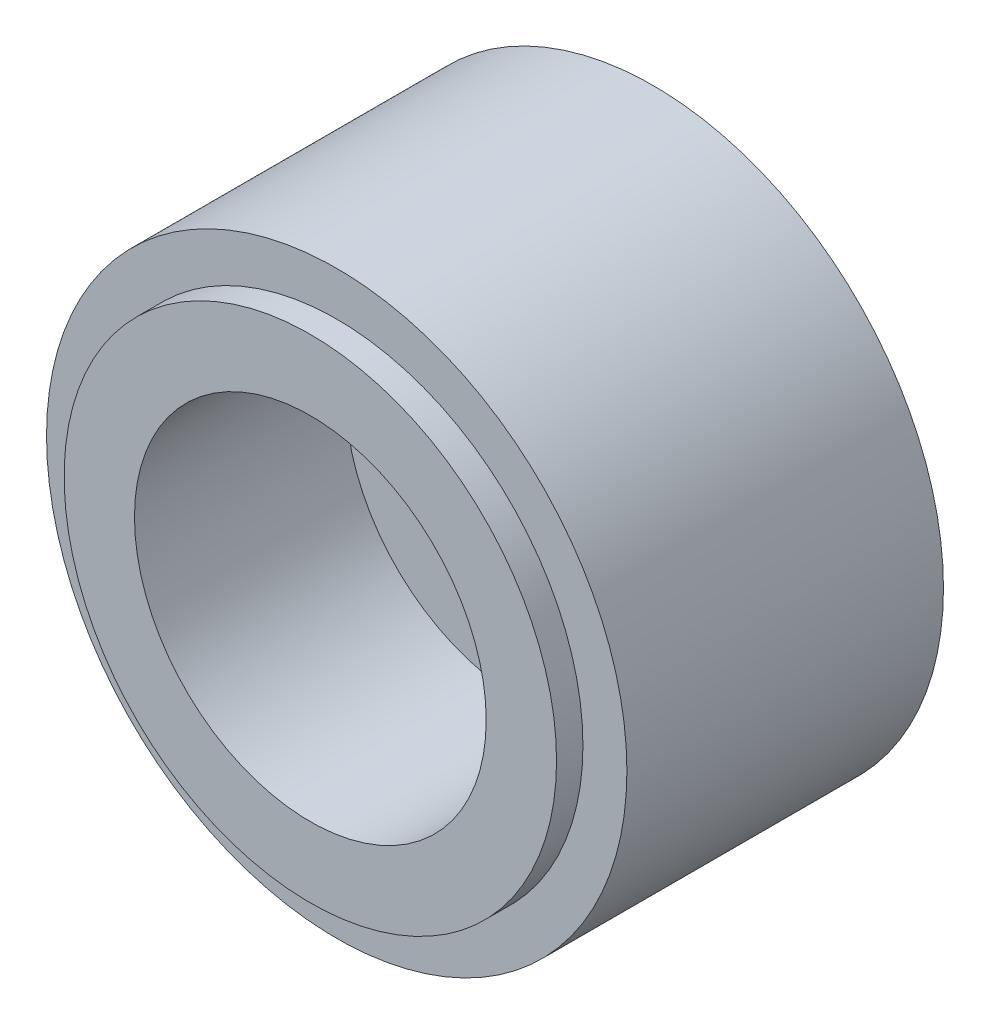
SolidWorks part; units mm, degrees
ref_plane "Front Plane" through (0, 0, 0) normal (0, 0, 1) x (1, 0, 0)
ref_plane "Top Plane" through (0, 0, 0) normal (0, 1, 0) x (1, 0, 0)
ref_plane "Right Plane" through (0, 0, 0) normal (1, 0, 0) x (0, 0, -1)
sketch "Sketch1" plane through (0, 0, 0) normal (0, 0, 1) x (1, 0, 0)
  circle A0 centre (0, 0) radius 14
  circle A1 centre (0, 0) radius 1.5
  dimension "D1" = 28
  dimension "D2" = 3
extrude "Boss-Extrude1" add sketch "Sketch1" along normal blind 1.5
sketch "Sketch2" plane through (0, 0, 1.5) normal (0, 0, 1) x (1, 0, 0)
  circle A0 centre (0, 0) radius 10.5
  circle A1 centre (0, 0) radius 1.5
  dimension "D1" = 21
extrude "Boss-Extrude2" add sketch "Sketch2" along normal blind 18
sketch "Sketch3" plane through (0, 0, 19.5) normal (0, 0, 1) x (1, 0, 0)
  circle A0 centre (0, 0) radius 1.5
  circle A1 centre (0, 0) radius 14
extrude "Boss-Extrude3" add sketch "Sketch3" along normal blind 1.5
sketch "Sketch4" plane through (0, 0, 21) normal (0, 0, 1) x (1, 0, 0)
  circle A0 centre (0, 0) radius 10
  dimension "D1" = 20
extrude "Cut-Extrude1" cut sketch "Sketch4" against normal blind 12
sketch "Sketch5" plane through (0, 0, 1.5) normal (0, 0, 1) x (1, 0, 0)
  circle A0 centre (0, 0) radius 10.5
  circle A1 centre (0, 0) radius 16.5
  dimension "D1" = 33
extrude "Boss-Extrude4" add sketch "Sketch5" along normal blind 18
